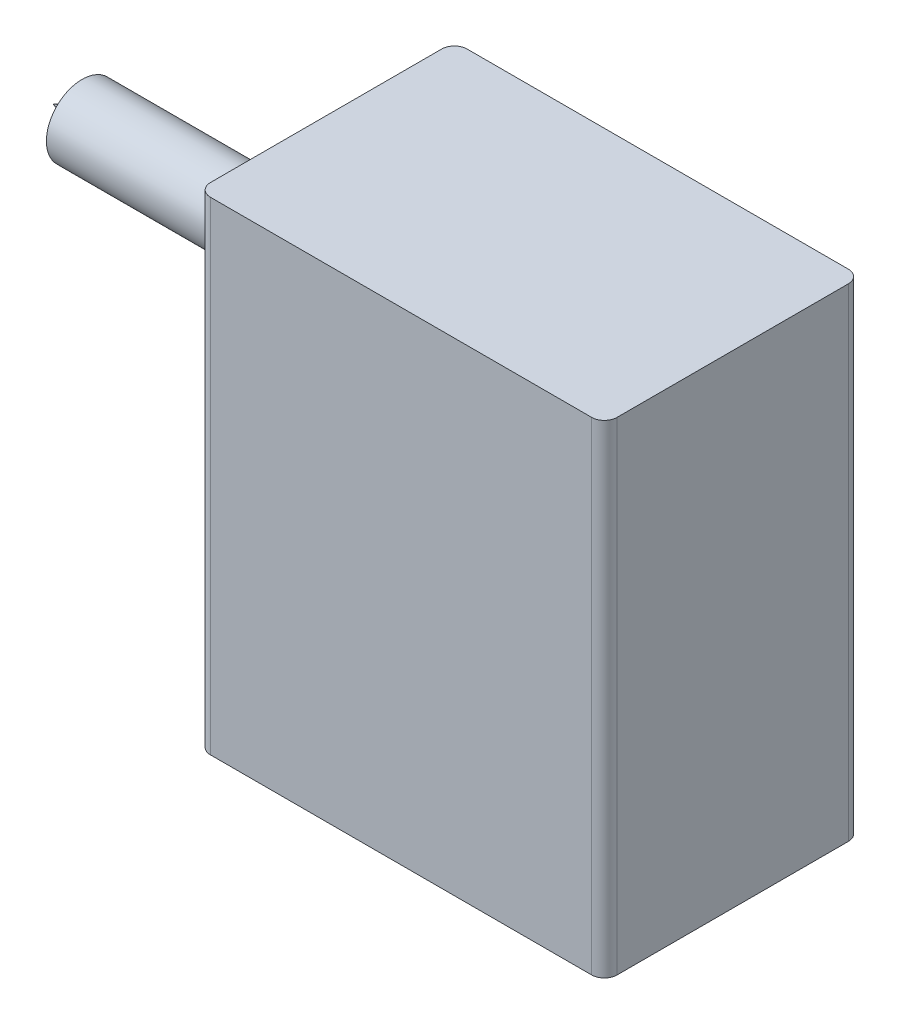
SolidWorks part; units mm, degrees
ref_plane "Płaszczyzna przednia" through (0, 0, 0) normal (0, 0, 1) x (1, 0, 0)
ref_plane "Płaszczyzna górna" through (0, 0, 0) normal (0, 1, 0) x (1, 0, 0)
ref_plane "Płaszczyzna prawa" through (0, 0, 0) normal (1, 0, 0) x (0, 0, -1)
sketch "Szkic1" plane through (0, 0, 0) normal (0, 0, 1) x (1, 0, 0)
  line L0 (340.5099, 191.3316) -> (340.5099, 571.3316)
  line L1 (340.5099, 571.3316) -> (20.5099, 571.3316)
  line L2 (20.5099, 571.3316) -> (20.5099, 191.3316)
  line L3 (20.5099, 191.3316) -> (340.5099, 191.3316)
  dimension "D1" = 320
  dimension "D2" = 380
extrude "Dodanie-wyciągnięcie1" add sketch "Szkic1" along normal blind 202 contours L1 L2 L3 L0
sketch "Szkic2" plane through (20.5099, 0, 0) normal (-1, 0, 0) x (0, 0, 1)
  circle A0 centre (101, 472.0912) radius 75.8204
extrude "Dodanie-wyciągnięcie2" add sketch "Szkic2" along normal blind 16
sketch "Szkic3" plane through (4.5099, 0, 0) normal (-1, 0, 0) x (0, 0, 1)
  circle A0 centre (101, 472.0912) radius 28.0512
extrude "Dodanie-wyciągnięcie3" add sketch "Szkic3" along normal blind 176
sketch "Szkic5" plane through (-171.4901, 0, 0) normal (-1, 0, 0) x (0, 0, 1)
  circle A0 centre (101, 472.0912) radius 8.3162
extrude "Dodanie-wyciągnięcie4" add sketch "Szkic5" along normal blind 36 draft 20
fillet "Zaokrąglenie1" radius 10 4 edges at (340.5099, 381.3316, 0) (340.5099, 381.3316, 202) (20.5099, 381.3316, 202) (20.5099, 381.3316, 0)
